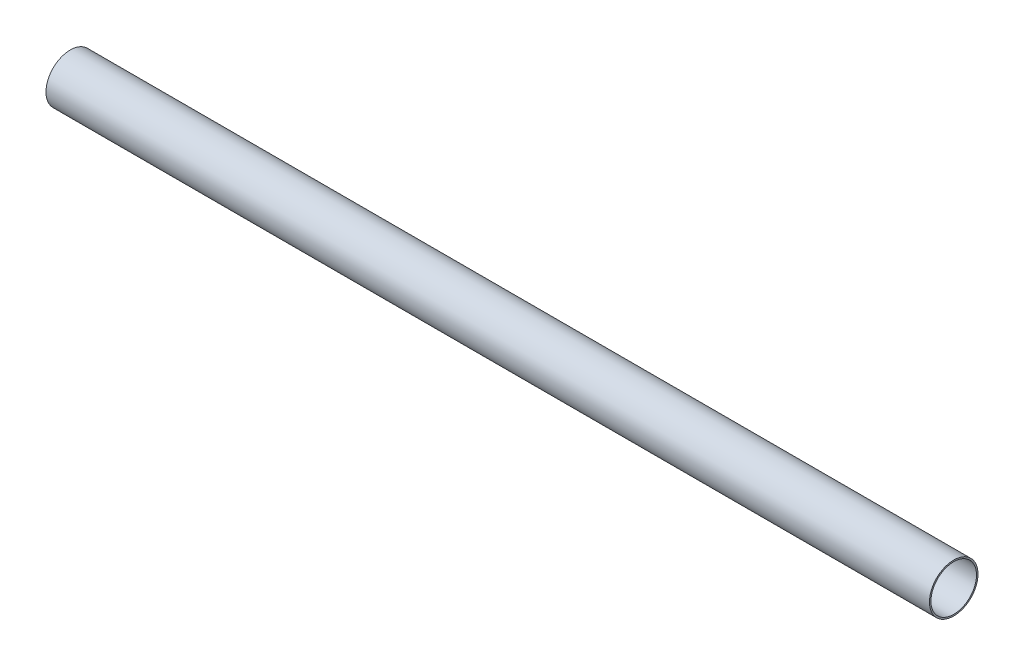
SolidWorks part; units mm, degrees
ref_plane "Front Plane" through (0, 0, 0) normal (0, 0, 1) x (1, 0, 0)
ref_plane "Top Plane" through (0, 0, 0) normal (0, 1, 0) x (1, 0, 0)
ref_plane "Right Plane" through (0, 0, 0) normal (1, 0, 0) x (0, 0, -1)
sketch "Sketch1" plane through (0, 0, 0) normal (0, 0, 1) x (1, 0, 0)
  line L0 (147.7757, 15.5) -> (-416.2243, 15.5)
  line L1 (-416.2243, 15.5) -> (-416.2243, 14.55)
  line L2 (-416.2243, 14.55) -> (147.7757, 14.55)
  line L3 (147.7757, 14.55) -> (147.7757, 15.5)
  line L4 (147.7757, 0) -> (-665.4102, 0) construction
  dimension "D1" = 14.55
  dimension "D2" = 15.5
  dimension "D3" = 564
  dimension "D4" = 0
revolve "Revolve1" add sketch "Sketch1" angle 360 about L4
